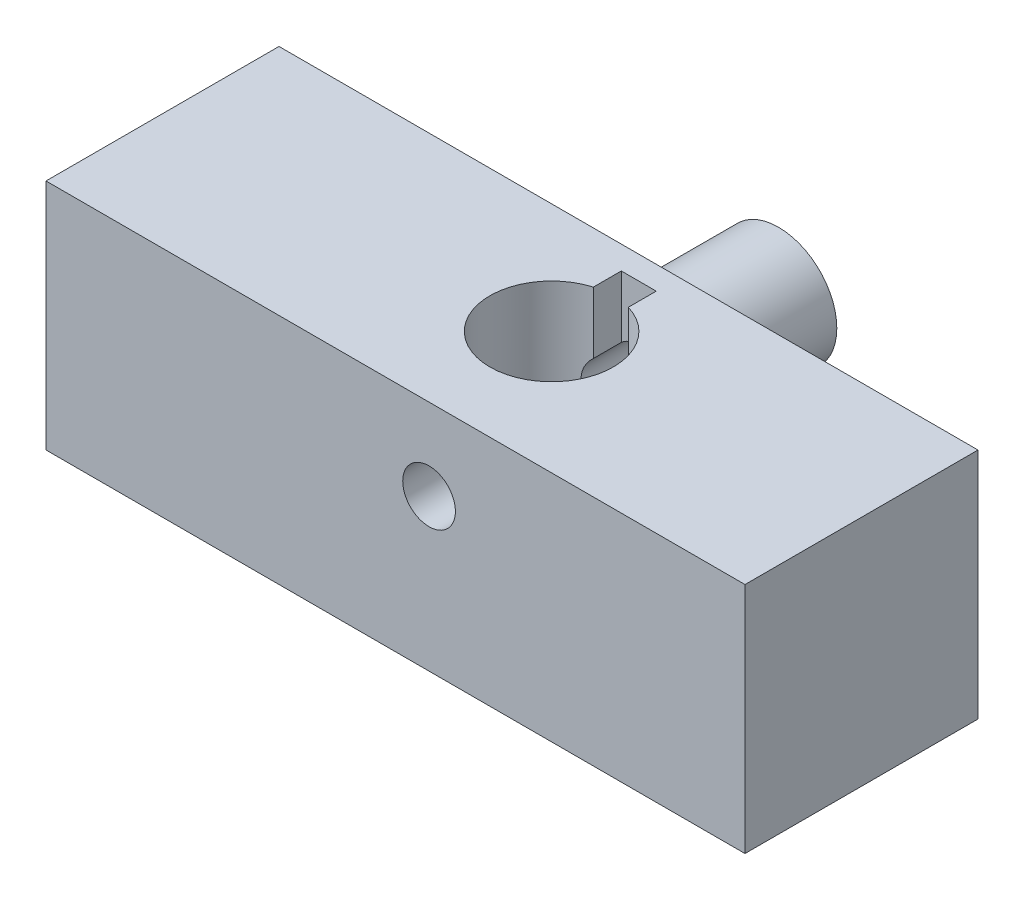
SolidWorks part; units mm, degrees
ref_plane "Front Plane" through (0, 0, 0) normal (0, 0, 1) x (1, 0, 0)
ref_plane "Top Plane" through (0, 0, 0) normal (0, 1, 0) x (1, 0, 0)
ref_plane "Right Plane" through (0, 0, 0) normal (1, 0, 0) x (0, 0, -1)
sketch "Sketch1" plane through (0, 0, 0) normal (0, 0, 1) x (1, 0, 0)
  line L0 (0, 2.3095) -> (0, 0) construction
  line L1 (-16.4407, 5.8095) -> (13.5593, 5.8095)
  line L2 (-16.4407, 5.8095) -> (-16.4407, -4.1905)
  line L3 (-16.4407, -4.1905) -> (13.5593, -4.1905)
  line L4 (13.5593, 5.8095) -> (13.5593, -4.1905)
  circle A0 centre (0, 2.3095) radius 2.5 construction
  circle A1 centre (0, 2.3095) radius 1.1303 construction
  dimension "D3" = 5
  dimension "D5" = 2.2606
  dimension "D1" = 10
  dimension "D2" = 30
  dimension "D4" = 3.5
extrude "Boss-Extrude1" add sketch "Sketch1" along normal blind 10
sketch "Sketch2" plane through (0, 0, 0) normal (0, 0, -1) x (-1, 0, 0)
  circle A0 centre (0, 2.3095) radius 2.5 construction
  circle A1 centre (0, 2.3095) radius 1.1303 construction
  circle A2 centre (0, 2.3095) radius 2.5
  circle A3 centre (0, 2.3095) radius 1.1303
extrude "4-40 screw space" add sketch "Sketch2" along normal blind 5
sketch "Sketch5" plane through (0, 0, -5) normal (0, 0, -1) x (-1, 0, 0)
  circle A0 centre (0, 2.3095) radius 1.1303 construction
  circle A1 centre (0, 2.3095) radius 1.1303
extrude "Cut-Extrude3" cut sketch "Sketch5" against normal through all
sketch "Sketch3" plane through (0, 5.8095, 0) normal (0, 1, 0) x (1, 0, 0)
  circle A0 centre (0, -4.7403) radius 2.65
  dimension "D1" = 5.3
extrude "Cut-Extrude1" cut sketch "Sketch3" against normal blind 8
sketch "Sketch4" plane through (0, 5.8095, 0) normal (0, 1, 0) x (1, 0, 0)
  line L0 (0, -7.3903) -> (0, -0.7772) construction
  line L2 (0.75, -1) -> (-0.75, -1)
  line L3 (0.75, -1) -> (0.75, -2.7782)
  line L4 (0.75, -2.7782) -> (-0.75, -2.7782)
  line L5 (-0.75, -1) -> (-0.75, -2.7782)
  line L6 (13.5593, 0) -> (-16.4407, 0) construction
  circle A0 centre (0, -4.7403) radius 2.65 construction
  dimension "D1" = 1
  dimension "D2" = 1.5
  dimension "D3" = 0.75
extrude "Cut-Extrude2" cut sketch "Sketch4" against normal blind 5
